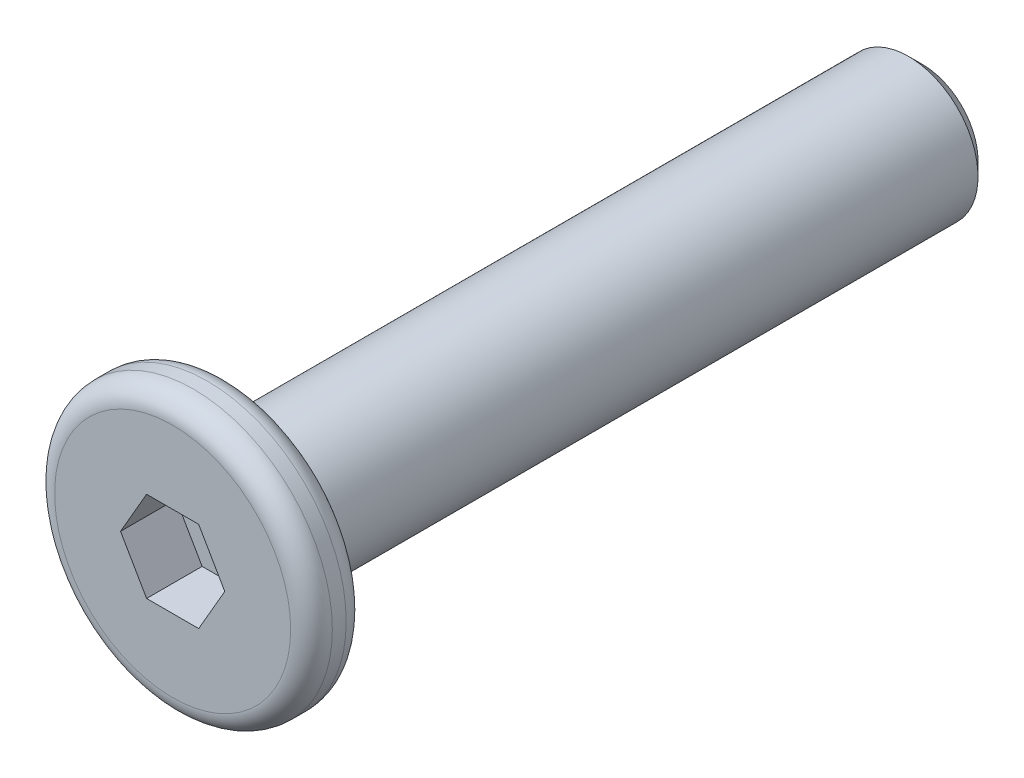
SolidWorks part; units mm, degrees
ref_plane "前视基准面" through (0, 0, 0) normal (0, 0, 1) x (1, 0, 0)
ref_plane "上视基准面" through (0, 0, 0) normal (0, 1, 0) x (1, 0, 0)
ref_plane "右视基准面" through (0, 0, 0) normal (1, 0, 0) x (0, 0, -1)
sketch "草图1" plane through (0, 0, 0) normal (0, 0, 1) x (1, 0, 0)
  circle A0 centre (0, 0) radius 2
  dimension "D1" = 4
extrude "凸台-拉伸1" add sketch "草图1" along normal mid plane 0.8
sketch "草图2" plane through (0, 0, -0.4) normal (0, 0, -1) x (-1, 0, 0)
  circle A0 centre (0, 0) radius 1
  dimension "D1" = 2
extrude "凸台-拉伸2" add sketch "草图2" along normal blind 10
chamfer "倒角1" distance 0.2 angle 45 1 edges at (-1, 0, -10.4)
sketch "草图3" plane through (0, 0, 0.4) normal (0, 0, 1) x (1, 0, 0)
  line L1 (0.7506, 0) -> (0.3753, 0.65)
  line L2 (0.3753, 0.65) -> (-0.3753, 0.65)
  line L3 (-0.3753, 0.65) -> (-0.7506, 0)
  line L4 (-0.7506, 0) -> (-0.3753, -0.65)
  line L5 (-0.3753, -0.65) -> (0.3753, -0.65)
  line L6 (0.3753, -0.65) -> (0.7506, 0)
  circle A0 centre (0, 0) radius 0.65 construction
  dimension "D1" = 1.3
extrude "切除-拉伸1" cut sketch "草图3" against normal blind 0.8
fillet "圆角2" radius 0.3 2 edges at (2, 0, -0.4) (2, 0, 0.4)
